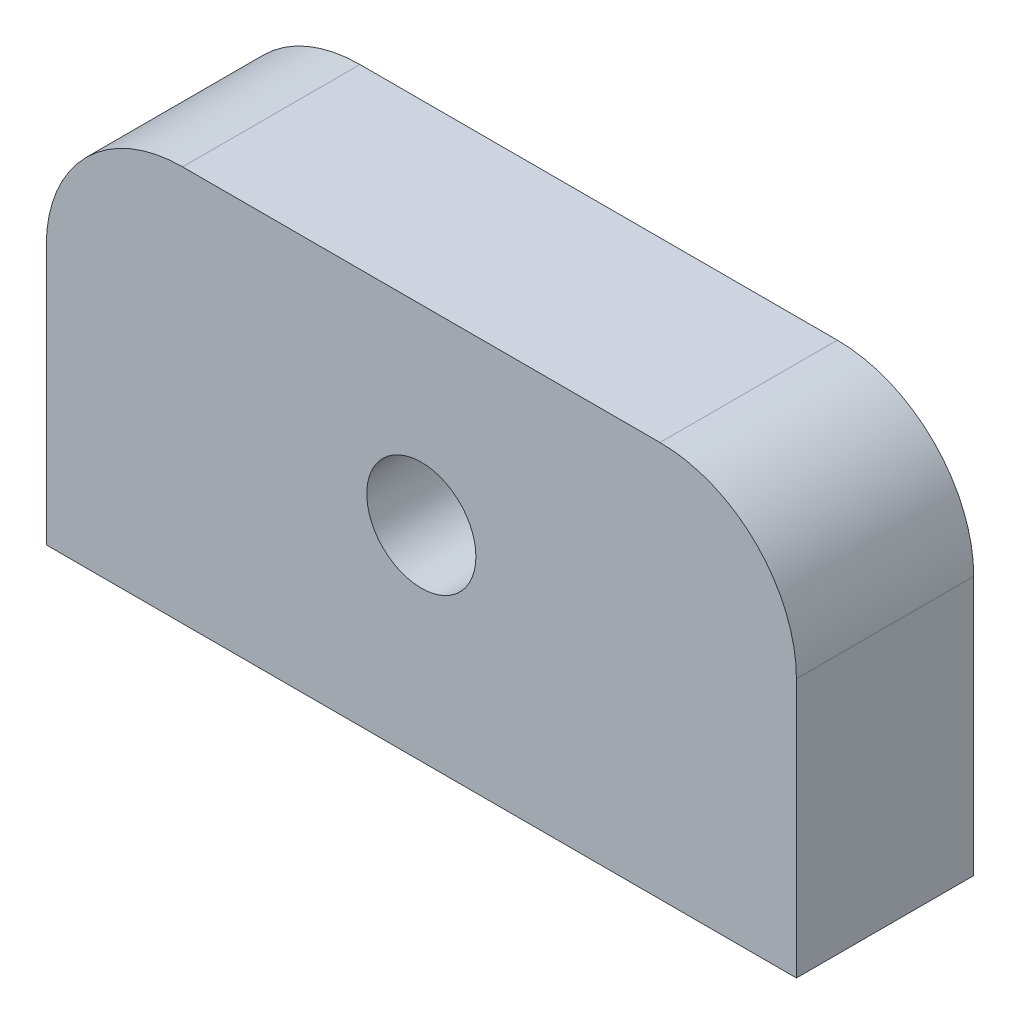
SolidWorks part; units mm, degrees
ref_plane "前视基准面" through (0, 0, 0) normal (0, 0, 1) x (1, 0, 0)
ref_plane "上视基准面" through (0, 0, 0) normal (0, 1, 0) x (1, 0, 0)
ref_plane "右视基准面" through (0, 0, 0) normal (1, 0, 0) x (0, 0, -1)
sketch "草图1" plane through (0, 0, 0) normal (0, 0, 1) x (1, 0, 0)
  line L1 (-24.3239, 11.7254) -> (30.6761, 11.7254)
  line L2 (-24.3239, 11.7254) -> (-24.3239, -17.2746)
  line L3 (-24.3239, -17.2746) -> (30.6761, -17.2746)
  line L4 (30.6761, 11.7254) -> (30.6761, -17.2746)
  dimension "D1" = 55
  dimension "D2" = 29
extrude "凸台-拉伸1" add sketch "草图1" along normal blind 13
sketch "草图2" plane through (0, 0, 13) normal (0, 0, 1) x (1, 0, 0)
  line L1 (-24.3239, 11.7254) -> (30.6761, 11.7254)
  line L2 (-24.3239, 11.7254) -> (-24.3239, -17.2746)
  line L3 (-24.3239, -17.2746) -> (30.6761, -17.2746)
  line L4 (30.6761, 11.7254) -> (30.6761, -17.2746)
  circle A0 centre (3.1761, -2.2746) radius 4
  dimension "D1" = 8
  dimension "D2" = 15
  dimension "D3" = 27.5
extrude "切除-拉伸1" cut sketch "草图2" against normal blind 13 flip side to cut
fillet "圆角1" radius 10 2 edges at (30.6761, 11.7254, 6.5) (-24.3239, 11.7254, 6.5)
